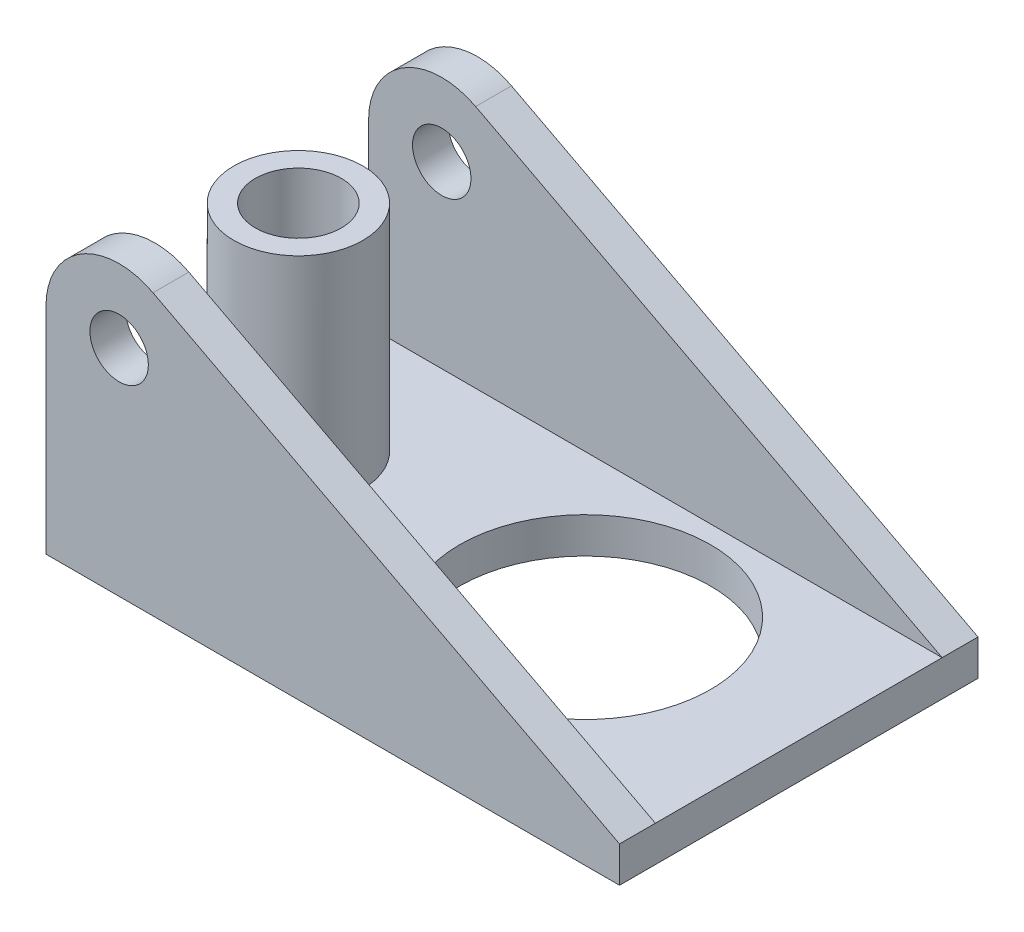
SolidWorks part; units mm, degrees
ref_plane "Front Plane" through (0, 0, 0) normal (0, 0, 1) x (1, 0, 0)
ref_plane "Top Plane" through (0, 0, 0) normal (0, 1, 0) x (1, 0, 0)
ref_plane "Right Plane" through (0, 0, 0) normal (1, 0, 0) x (0, 0, -1)
sketch "Sketch3" plane through (0, 0, 0) normal (0, 0, 1) x (1, 0, 0)
  line L0 (0, 0) -> (0, 25)
  line L1 (14.9277, 34.0382) -> (80, 0)
  line L3 (0, 0) -> (0, -5)
  line L4 (0, -5) -> (80, -5)
  line L5 (80, -5) -> (80, 0)
  arc A0 (0, 25) -> (14.9277, 34.0382) centre (10.2, 25) cw
  circle A1 centre (10.2, 25) radius 4.075
  dimension "D1" = 10.2
  dimension "D2" = 8.15
  dimension "D3" = 25
  dimension "D4" = 80
  dimension "D5" = 5
extrude "Boss-Extrude3" add sketch "Sketch3" along normal blind 50
ref_plane "Plane1" through (0, 0, 45) normal (0, 0, 1) x (1, 0, 0)
sketch "Sketch6" plane through (0, 0, 45) normal (0, 0, 1) x (1, 0, 0)
  line L1 (0, 25) -> (0, -5) construction
  line L2 (80, 0) -> (14.9277, 34.0382) construction
  line L4 (0, 25) -> (0, 0)
  line L5 (80, 0) -> (14.9277, 34.0382)
  line L6 (0, 0) -> (80, 0)
  arc A0 (14.9277, 34.0382) -> (0, 25) centre (10.2, 25) ccw construction
  arc A1 (14.9277, 34.0382) -> (0, 25) centre (10.2, 25) ccw
extrude "Cut-Extrude1" cut sketch "Sketch6" against normal offset from surface (40 mm away) 5 up to face at (34.4762, 10.6489, 0)
sketch "Sketch8" plane through (0, 0, 0) normal (0, 1, 0) x (1, 0, 0)
  line L0 (0, -5) -> (0, -45) construction
  circle A0 centre (10.2, -25) radius 6
  circle A1 centre (50.2, -25) radius 17.5
  point P4 (0, -25)
  dimension "D1" = 12
  dimension "D3" = 35
  dimension "D2" = 10.2
  dimension "D4" = 40
extrude "Cut-Extrude2" cut sketch "Sketch8" against normal through all contours A0 | A1
sketch "Sketch9" plane through (0, 0, 0) normal (0, 1, 0) x (1, 0, 0)
  circle A0 centre (10.2, -25) radius 6
  circle A1 centre (10.2, -25) radius 9
  circle A4 centre (10.2, -25) radius 6 construction
  point P5 (0, 0)
  point P6 (0, 0)
  dimension "D1" = 18
extrude "Boss-Extrude4" add sketch "Sketch9" along normal blind 30
equation "\"Width\"=50"
equation "\"D1@Boss-Extrude3\"=\"Width\""
equation "\"Thicknes\"=5"
equation "\"D1@Cut-Extrude1\"=\"Thicknes\""
